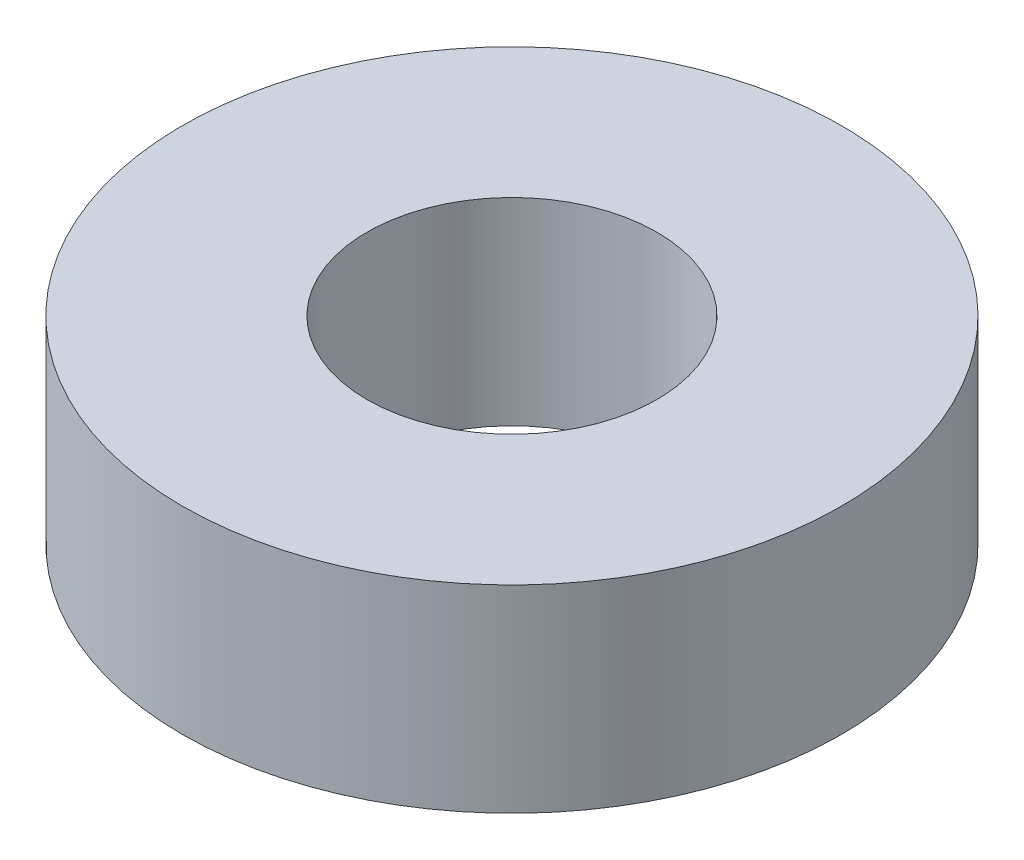
SolidWorks part; units mm, degrees
ref_plane "Front Plane" through (0, 0, 0) normal (0, 0, 1) x (1, 0, 0)
ref_plane "Top Plane" through (0, 0, 0) normal (0, 1, 0) x (1, 0, 0)
ref_plane "Right Plane" through (0, 0, 0) normal (1, 0, 0) x (0, 0, -1)
sketch "Sketch1" plane through (0, 0, 0) normal (0, 1, 0) x (1, 0, 0)
  circle A0 centre (0, 0) radius 5
  circle A1 centre (0, 0) radius 2.2
  dimension "D1" = 4.4
  dimension "D2" = 10
extrude "Boss-Extrude1" add sketch "Sketch1" along normal blind 3
